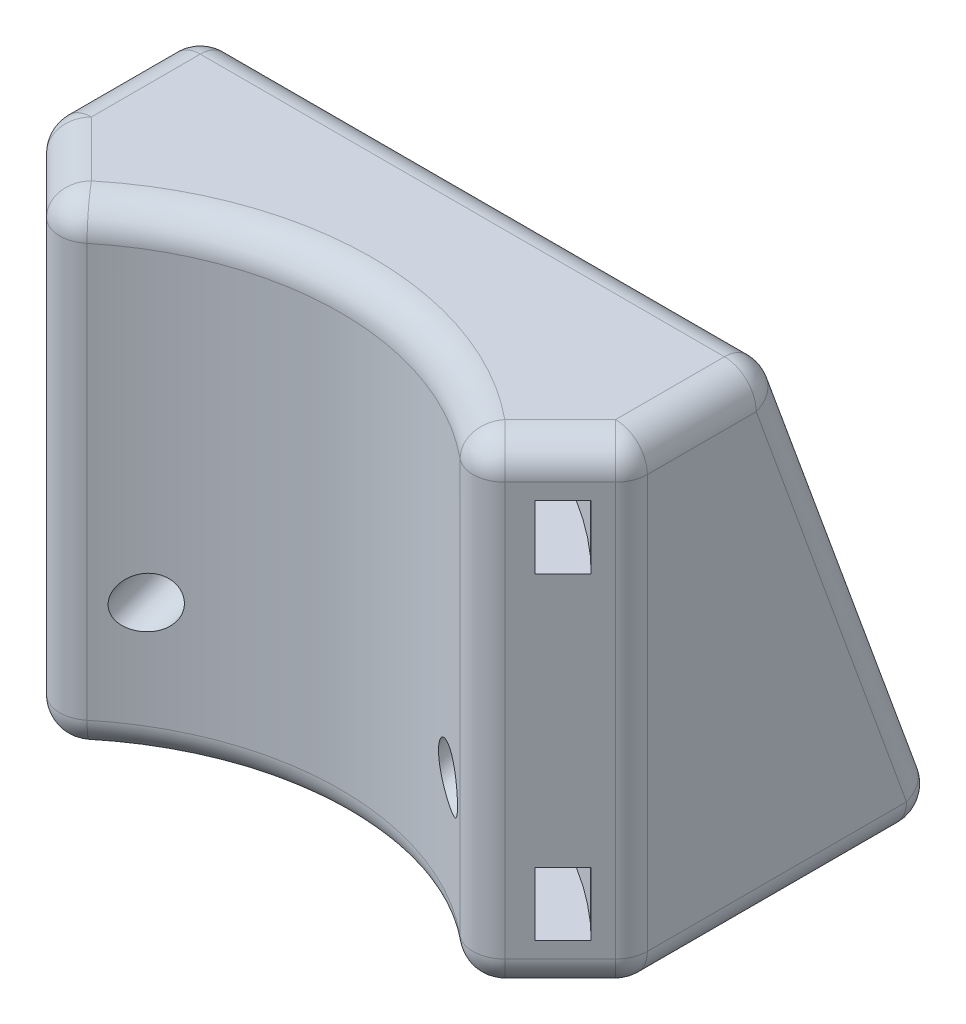
SolidWorks part; units mm, degrees
ref_plane "Front" through (0, 0, 0) normal (0, 0, 1) x (1, 0, 0)
ref_plane "Top" through (0, 0, 0) normal (0, 1, 0) x (1, 0, 0)
ref_plane "Right" through (0, 0, 0) normal (1, 0, 0) x (0, 0, -1)
sketch "Sketch3" plane through (0, 0, 0) normal (0, 1, 0) x (1, 0, 0)
  line L0 (0, 18.5) -> (0, 38.5) construction
  line L1 (-18.5, 38.5) -> (18.5, 38.5)
  line L2 (18.5, 38.5) -> (18.5, 18.5)
  line L3 (13.0815, 13.0815) -> (18.5, 18.5)
  line L4 (-18.5, 18.5) -> (18.5, 18.5) construction
  line L5 (-13.0815, 13.0815) -> (-18.5, 18.5)
  line L6 (-18.5, 38.5) -> (-18.5, 18.5)
  arc A0 (-13.0815, 13.0815) -> (13.0815, 13.0815) centre (0, 0) cw
  ellipse E0 centre (0, 0) end of major axis (0, -18.5) minor radius 18.5 construction
  dimension "D1" = 37
  dimension "D2" = 37
  dimension "D3" = 20
  dimension "D4" = 135
extrude "Boss-Extrude1" add sketch "Sketch3" along normal blind 30
ref_plane "Plane1" through (0, 12.3737, -33.9964) normal (0, 0.342, -0.9397) x (-1, 0, 0)
split "Split1" trim tools "Plane1" bodies to split 101 resulting bodies 103
sketch "Sketch4" plane through (0, 12.3737, -33.9964) normal (0, 0.342, -0.9397) x (-1, 0, 0)
  line L0 (18.5, -13.1678) -> (-18.5, 18.7576) construction
  line L1 (18.5, 18.7576) -> (-18.5, -13.1678) construction
  line L2 (18.5, -13.1678) -> (18.5, 18.7576) construction
  line L3 (18.5, 18.7576) -> (-18.5, 18.7576) construction
  line L4 (0, 2.7949) -> (-9.5, 2.7949) construction
  line L5 (0, 2.7949) -> (9.5, 2.7949) construction
  circle A0 centre (9.5, 2.7949) radius 1.5
  circle A1 centre (-9.5, 2.7949) radius 1.5
  point P14 (0, 2.7949)
  dimension "D2" = 3
  dimension "D1" = 19
extrude "Cut-Extrude1" cut sketch "Sketch4" against normal through all
ref_axis "Axis1" through (0, 30, 0) along (0, -1, 0)
sketch "Sketch5" plane through (0, 0, 0) normal (1, 0, 0) x (0, 0, -1)
  line L0 (0, 0) -> (23, 0) construction
  line L2 (23, 0) -> (23, 30) construction
  line L4 (21.75, 3) -> (24.25, 3)
  line L5 (21.75, 3) -> (21.75, 7)
  line L6 (21.75, 7) -> (24.25, 7)
  line L7 (24.25, 3) -> (24.25, 7)
  line L8 (21.75, 3) -> (24.25, 7) construction
  line L9 (21.75, 7) -> (24.25, 3) construction
  line L10 (21.75, 23) -> (24.25, 23)
  line L11 (21.75, 23) -> (21.75, 27)
  line L12 (21.75, 27) -> (24.25, 27)
  line L13 (24.25, 23) -> (24.25, 27)
  line L14 (21.75, 23) -> (24.25, 27) construction
  line L15 (21.75, 27) -> (24.25, 23) construction
  line L16 (27.5809, 30) -> (18.5, 30) construction
  point P3 (23, 25)
  point P4 (23, 5)
  point P14 (21.25, 24.9724)
  point P15 (23, 15)
  dimension "D1" = 23
  dimension "D2" = 2.5
  dimension "D3" = 4
  dimension "D4" = 8
  dimension "D5" = 8
  dimension "D6" = 4
fillet "Fillet1" radius 2 18 edges at (-15.7907, 30, -15.7907) (-18.5, 30, -23.0404) (18.5, 30, -23.0404) (0, 30, -27.5809) (0, 30, -18.5) (-13.0815, 15, -13.0815) (-15.7907, 0, -15.7907) (-18.5, 15, -18.5) (-18.5, 15, -33.0404) (-18.5, 0, -28.5) (0, 0, -38.5) (18.5, 0, -28.5) (18.5, 15, -33.0404) (15.7907, 30, -15.7907) (18.5, 15, -18.5) (15.7907, 0, -15.7907) (0, 0, -18.5) (13.0815, 15, -13.0815)
revolve "Cut-Revolve1" cut sketch "Sketch5" angle 360 about axis through (0, 30, 0) along (0, -1, 0)
equation "\"tubeForward\"= 35mm"
equation "\"tubeSkew\"= 35mm"
equation "\"ultiTol\"= 2mm"
equation "\"D1@Sketch3\"=\"tubeForward\"+\"ultiTol\""
equation "\"D2@Sketch3\"=\"tubeSkew\"+\"ultiTol\""
equation "\"D6@Sketch5\"=\"D3@Sketch5\""
